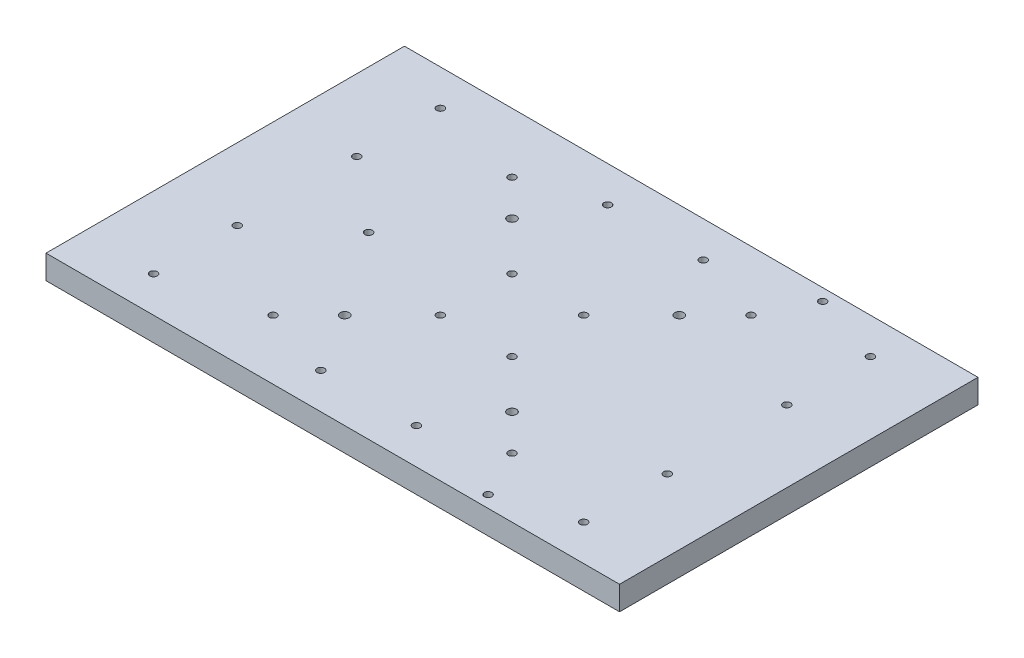
SolidWorks part; units mm, degrees
ref_plane "Front Plane" through (0, 0, 0) normal (0, 0, 1) x (1, 0, 0)
ref_plane "Top Plane" through (0, 0, 0) normal (0, 1, 0) x (1, 0, 0)
ref_plane "Right Plane" through (0, 0, 0) normal (1, 0, 0) x (0, 0, -1)
sketch "Sketch2" plane through (0, 0, 0) normal (0, 1, 0) x (1, 0, 0)
  line L1 (-304.8, 190.5) -> (304.8, 190.5)
  line L2 (-304.8, 190.5) -> (-304.8, -190.5)
  line L3 (-304.8, -190.5) -> (304.8, -190.5)
  line L4 (304.8, 190.5) -> (304.8, -190.5)
  line L5 (-304.8, 190.5) -> (304.8, -190.5) construction
  line L6 (-304.8, -190.5) -> (304.8, 190.5) construction
  point P0 (0, 0)
  dimension "D1" = 381
  dimension "D2" = 609.6
extrude "Boss-Extrude1" add sketch "Sketch2" along normal mid plane 25.4
sketch "Sketch3" plane through (0, 12.7, 0) normal (0, 1, 0) x (1, 0, 0)
  circle A0 centre (88.9, 88.9) radius 4.7625
  dimension "D1" = 88.9
  dimension "D2" = 88.9
extrude "Cut-Extrude1" cut sketch "Sketch3" against normal through all
hole_wizard "3/8-16 Tapped Hole1" positions "Sketch5" profile "Sketch4" tap size "3/8-16" standard "ANSI Inch" end condition up to next
sketch "Sketch5" plane through (0, 12.7, 0) normal (0, 1, 0) x (1, 0, 0)
  point P0 (127, 127)
  point P5 (38.1, 38.1)
  point P7 (228.6, 63.5)
  point P9 (228.6, 152.4)
  point P11 (50.8, 152.4)
  dimension "D1" = 127
  dimension "D2" = 127
  dimension "D3" = 228.6
  dimension "D4" = 50.8
  dimension "D5" = 88.9
  dimension "D6" = 63.5
  dimension "D7" = 38.1
  dimension "D8" = 38.1
sketch "Sketch4" plane through (127, 12.7, -127) normal (1, 0, 0) x (0, 0, 1)
  line L0 (0, 0) -> (0, 25.401)
  line L1 (0, 25.401) -> (3.9687, 25.401)
  line L2 (3.9687, 25.401) -> (3.9687, 0)
  line L5 (3.9687, 0) -> (0, 0)
  line L11 (0, -6.35) -> (0, 107.95) construction
  dimension "Thru Tap Drill Dia." = 7.9375
  dimension "Thru Tap Drill Depth" = 25.401
cosmetic thread "Hole Thread1" parameters "D2"=9.525
cosmetic thread "Hole Thread5" parameters "D2"=9.525
cosmetic thread "Hole Thread6" parameters "D2"=9.525
cosmetic thread "Hole Thread7" parameters "D2"=9.525
cosmetic thread "Hole Thread8" parameters "D2"=9.525
hole_wizard "3/8-16 Tapped Hole2" positions "Sketch7" profile "Sketch6" tap size "3/8-16" standard "ANSI Inch" end condition up to next
sketch "Sketch7" plane through (0, 12.7, 0) normal (0, 1, 0) x (1, 0, 0)
  point P0 (152.4, 177.8)
  point P2 (152.4, -177.8)
  point P4 (-152.4, 0)
  dimension "D1" = 152.4
  dimension "D2" = 152.4
  dimension "D3" = 177.8
  dimension "D4" = 177.8
sketch "Sketch6" plane through (152.4, 12.7, -177.8) normal (1, 0, 0) x (0, 0, 1)
  line L0 (0, 0) -> (0, 25.4)
  line L1 (0, 25.4) -> (3.9687, 25.4)
  line L2 (3.9687, 25.4) -> (3.9687, 0)
  line L5 (3.9687, 0) -> (0, 0)
  line L11 (0, -6.35) -> (0, 107.95) construction
  dimension "Thru Tap Drill Dia." = 7.9375
  dimension "Thru Tap Drill Depth" = 25.4
cosmetic thread "Hole Thread2" parameters "D2"=9.525
cosmetic thread "Hole Thread3" parameters "D2"=9.525
cosmetic thread "Hole Thread4" parameters "D2"=9.525
mirror "Mirror1" about plane through (0, 0, 0) normal (0, 0, 1) of "3/8-16 Tapped Hole1", "Cut-Extrude1"
mirror "Mirror2" about plane through (0, 0, 0) normal (1, 0, 0) of "Mirror1", "3/8-16 Tapped Hole1", "Cut-Extrude1"
